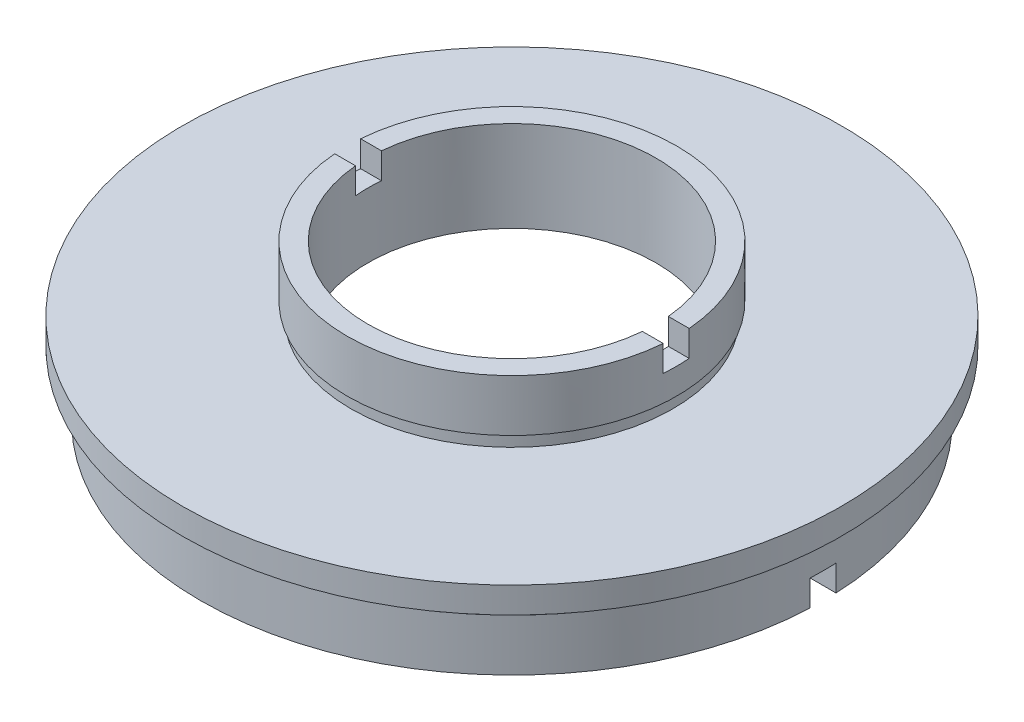
SolidWorks part; units mm, degrees
ref_plane "前视基准面" through (0, 0, 0) normal (0, 0, 1) x (1, 0, 0)
ref_plane "上视基准面" through (0, 0, 0) normal (0, 1, 0) x (1, 0, 0)
ref_plane "右视基准面" through (0, 0, 0) normal (1, 0, 0) x (0, 0, -1)
sketch "草图1" plane through (0, 0, 0) normal (0, 0, 1) x (1, 0, 0)
  line L0 (0, 22.6775) -> (0, 0) construction
  line L1 (-11.1, 12) -> (-12.7, 12)
  line L2 (-12.7, 12) -> (-12.7, 8)
  line L3 (-12.7, 8) -> (-12.4, 8)
  line L4 (-12.4, 8) -> (-12.4, 7)
  line L5 (-12.4, 7) -> (-25.4, 7)
  line L6 (-25.4, 7) -> (-25.4, 5)
  line L7 (-25.4, 5) -> (-23.5, 5)
  line L8 (-23.5, 5) -> (-23.5, 4)
  line L9 (-23.5, 4) -> (-24, 4)
  line L10 (-24, 4) -> (-24, 0)
  line L11 (-24, 0) -> (-20.5, 0)
  line L12 (-20.5, 0) -> (-20.5, 4)
  line L13 (-11.1, 5) -> (-21.1, 5)
  line L14 (-21.1, 5) -> (-21.1, 4)
  line L15 (-21.1, 4) -> (-20.5, 4)
  line L16 (-11.1, 12) -> (-11.1, 5)
  point P3 (-20.8, 4)
  point P5 (-25.4, 6)
  dimension "D2" = 1
  dimension "D3" = 1
  dimension "D4" = 5
  dimension "D5" = 5
  dimension "D6" = 12.7
  dimension "D7" = 25.4
  dimension "D8" = 24
  dimension "D9" = 23.5
  dimension "D10" = 12.4
  dimension "D11" = 20.5
  dimension "D12" = 0
  dimension "D13" = 21.1
  dimension "D14" = 11.1
  dimension "D15" = 12
  dimension "D16" = 7
  dimension "D17" = 1
revolve "旋转1" add sketch "草图1" angle 360 about L0
cosmetic thread "装饰螺纹线1" parameters "D2"=24.4
cosmetic thread "装饰螺纹线2" parameters "D2"=47
cosmetic thread "装饰螺纹线3" parameters "D2"=42
cosmetic thread "装饰螺纹线4" parameters "D2"=23.2
sketch "草图2" plane through (0, 0, 0) normal (1, 0, 0) x (0, 0, -1)
  line L0 (20.5, 12) -> (-20.5, 12) construction
  line L1 (-1, 13.594) -> (1, 13.594)
  line L2 (-1, 13.594) -> (-1, 10)
  line L3 (-1, 10) -> (1, 10)
  line L4 (1, 13.594) -> (1, 10)
  line L5 (-1, 2) -> (1, 2)
  line L6 (-1, 2) -> (-1, -4.6679)
  line L7 (-1, -4.6679) -> (1, -4.6679)
  line L8 (1, 2) -> (1, -4.6679)
  dimension "D1" = 2
  dimension "D2" = 1
  dimension "D3" = 2
  dimension "D4" = 1
  dimension "D5" = 2
  dimension "D6" = 2
extrude "切除-拉伸1" cut sketch "草图2" against normal mid plane 79
